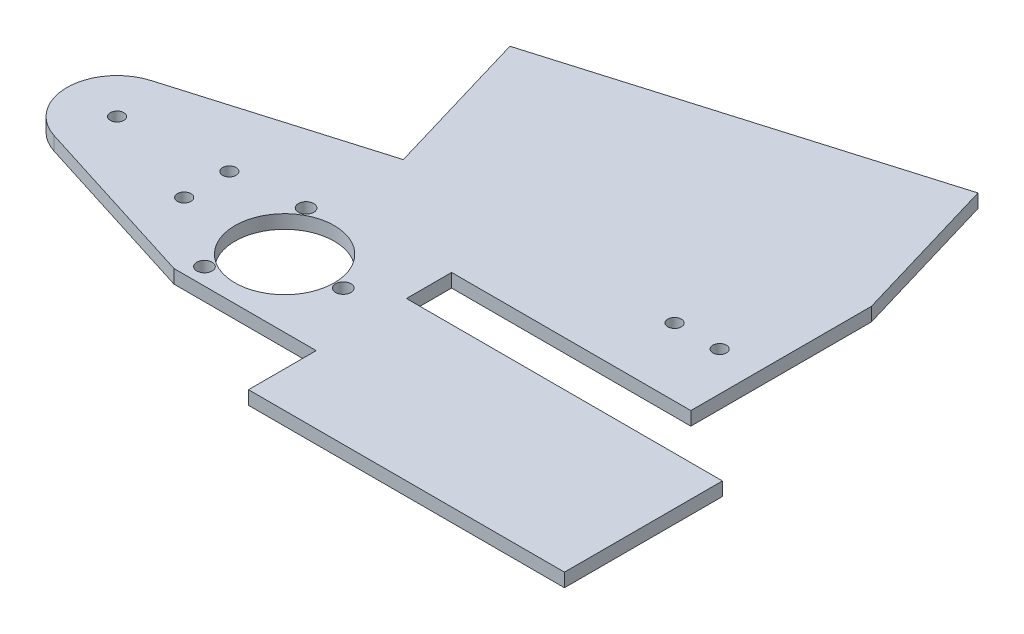
SolidWorks part; units mm, degrees
ref_plane "Plan de face" through (0, 0, 0) normal (0, 0, 1) x (1, 0, 0)
ref_plane "Plan de dessus" through (0, 0, 0) normal (0, 1, 0) x (1, 0, 0)
ref_plane "Plan de droite" through (0, 0, 0) normal (1, 0, 0) x (0, 0, -1)
sketch "Esquisse3" plane through (0, 0, 0) normal (0, -1, 0) x (1, 0, 0)
  line L0 (-464.8441, -40.3599) -> (-411.8441, -40.3599)
  line L1 (-353.8403, -40.3599) -> (-503.8403, -40.3599) construction
  line L2 (-496.3441, -10.3599) -> (-535.1601, -22.5947)
  line L3 (-534.9757, -43.8814) -> (-491.8441, -56.6594)
  line L4 (-491.8441, -56.6594) -> (-501.786, -90.2177)
  line L6 (-421.786, -113.9182) -> (-411.8441, -80.3599)
  line L7 (-411.8441, -40.3599) -> (-411.8441, -80.3599)
  line L8 (-501.786, -90.2177) -> (-421.786, -113.9182)
  line L9 (-464.8441, -10.3599) -> (-496.3441, -10.3599)
  line L10 (-464.8441, -10.3599) -> (-464.8441, 4.6401)
  line L11 (-464.8441, 4.6401) -> (-394.8441, 4.6401)
  line L12 (-394.8441, -30.3599) -> (-394.8441, 4.6401)
  line L14 (-464.8441, -30.3599) -> (-394.8441, -30.3599)
  line L16 (-464.8441, -30.3599) -> (-464.8441, -40.3599)
  circle A0 centre (-531.8141, -33.2099) radius 1.5
  circle A1 centre (-508.8441, -35.1135) radius 1.5
  circle A2 centre (-508.8441, -25.1135) radius 1.5
  arc A3 (-535.1601, -22.5947) -> (-534.9757, -43.8814) centre (-531.8141, -33.2099) ccw
  circle A4 centre (-486.8441, -25.3599) radius 11
  circle A5 centre (-473.8441, -25.3599) radius 1.7
  circle A6 centre (-493.3441, -36.6182) radius 1.7
  circle A7 centre (-493.3441, -14.1015) radius 1.7
  circle A8 centre (-420.4555, -55.3599) radius 1.5
  circle A9 centre (-430.4555, -55.3599) radius 1.5
  point P8 (0, 0)
  dimension "D1" = 3
  dimension "D2" = 3
  dimension "D3" = 3
  dimension "D7" = 3
  dimension "D5" = 13
  dimension "D13" = 10
  dimension "D15" = 15
  dimension "D17" = 11.13
  dimension "D9" = 15
  dimension "D20" = 8.6114
  dimension "D4" = 22
  dimension "D11" = 3.4
  dimension "D25" = 3
  dimension "D32" = 3
  dimension "D6" = 22.97
  dimension "D8" = 35
  dimension "D10" = 22
  dimension "D12" = 3
  dimension "D14" = 14.7536
  dimension "D16" = 22.85
  dimension "D18" = 70
  dimension "D19" = 20
  dimension "D21" = 40
  dimension "D23" = 35
  dimension "D24" = 80
  dimension "D26" = 53
  dimension "D28" = 10
  dimension "D29" = 10
  dimension "D31" = 92
extrude "Boss.-Extru.3" add sketch "Esquisse3" along normal blind 3 separate body
